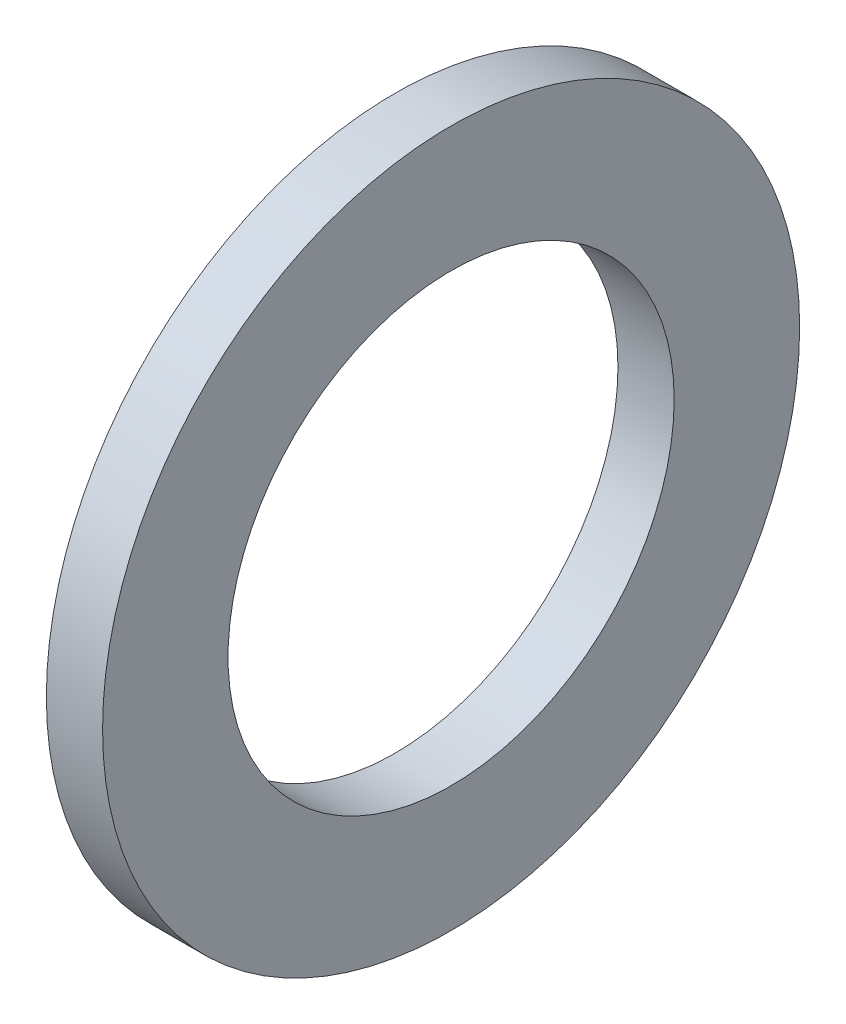
SolidWorks part; units mm, degrees
ref_plane "Front Plane" through (0, 0, 0) normal (0, 0, 1) x (1, 0, 0)
ref_plane "Top Plane" through (0, 0, 0) normal (0, 1, 0) x (1, 0, 0)
ref_plane "Right Plane" through (0, 0, 0) normal (1, 0, 0) x (0, 0, -1)
sketch "Sketch1" plane through (0, 0, 0) normal (1, 0, 0) x (0, 0, -1)
  circle A0 centre (0, 0) radius 19.8438
  circle A1 centre (0, 0) radius 12.7
  dimension "OD" = 39.6875
  dimension "Shaft Dia" = 25.4
extrude "Extrude1" add sketch "Sketch1" along normal blind 3.2004
